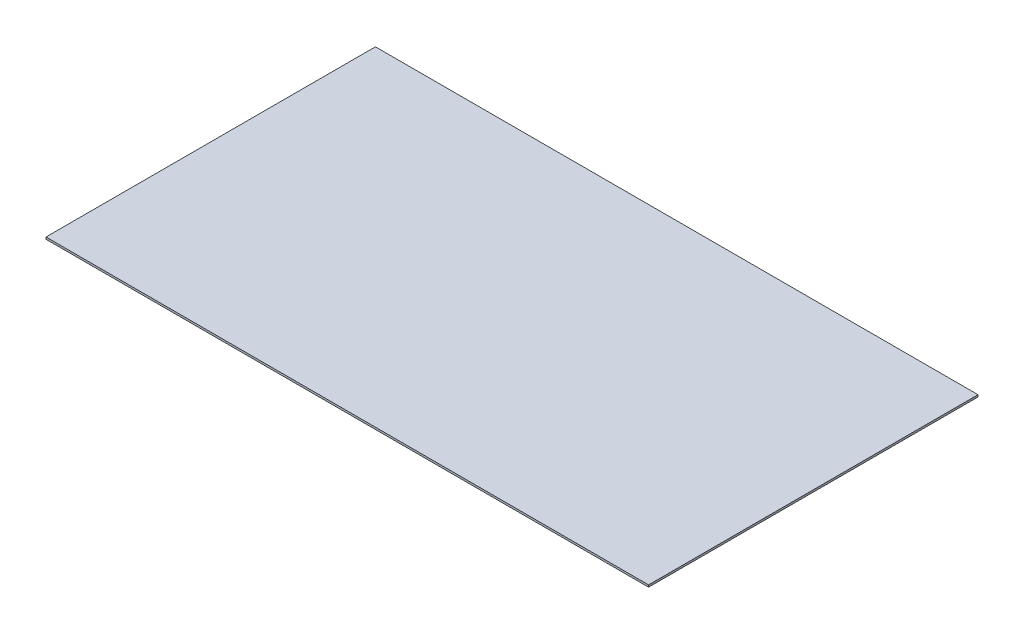
SolidWorks part; units mm, degrees
material "PC High Viscosity"
ref_plane "Front Plane" through (0, 0, 0) normal (0, 0, 1) x (1, 0, 0)
ref_plane "Top Plane" through (0, 0, 0) normal (0, 1, 0) x (1, 0, 0)
ref_plane "Right Plane" through (0, 0, 0) normal (1, 0, 0) x (0, 0, -1)
sketch "Sketch1" plane through (0, 0, 0) normal (0, 1, 0) x (1, 0, 0)
  line L1 (-238.125, 130.175) -> (238.125, 130.175)
  line L2 (-238.125, 130.175) -> (-238.125, -130.175)
  line L3 (-238.125, -130.175) -> (238.125, -130.175)
  line L4 (238.125, 130.175) -> (238.125, -130.175)
  line L5 (-238.125, 130.175) -> (238.125, -130.175) construction
  line L6 (-238.125, -130.175) -> (238.125, 130.175) construction
  point P0 (0, 0)
  dimension "D1" = 476.25
  dimension "D2" = 260.35
extrude "Boss-Extrude1" add sketch "Sketch1" along normal blind 1.5875
